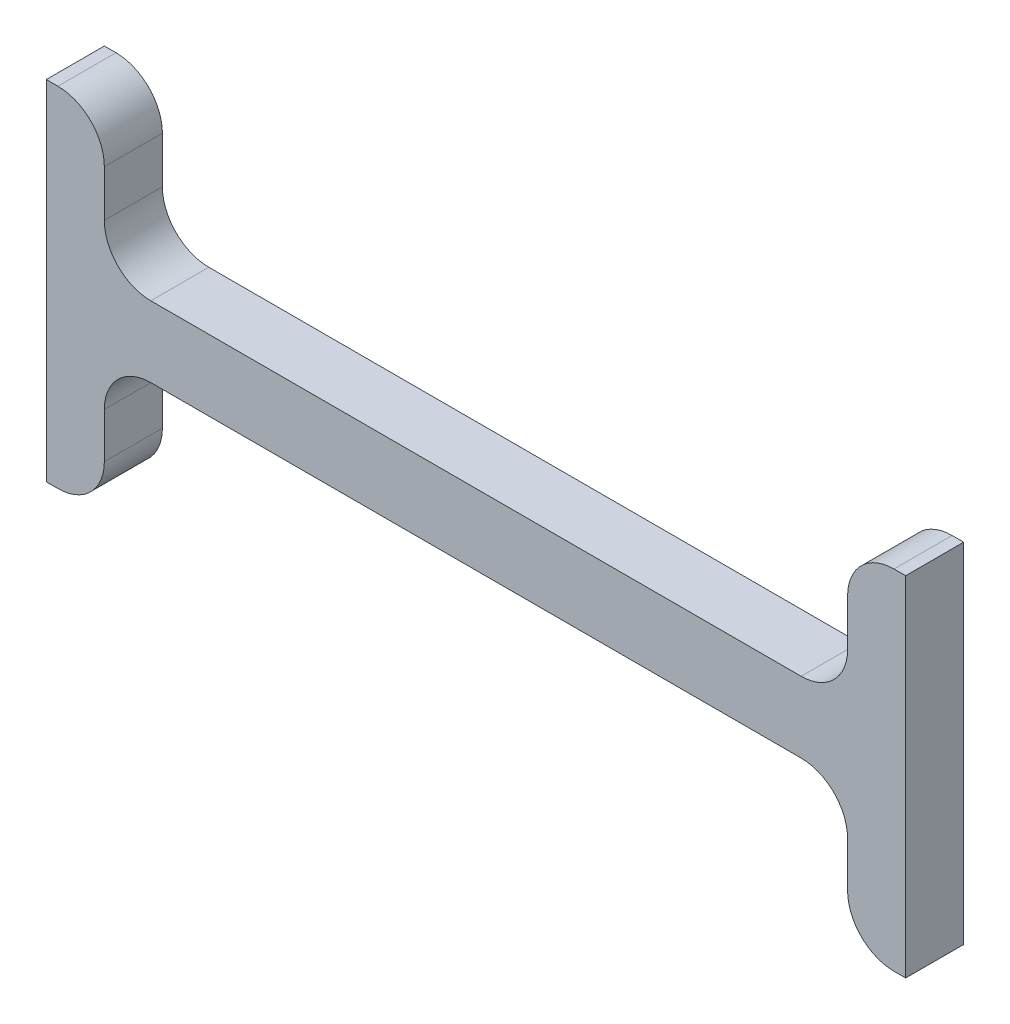
SolidWorks part; units mm, degrees
ref_plane "Front Plane" through (0, 0, 0) normal (0, 0, 1) x (1, 0, 0)
ref_plane "Top Plane" through (0, 0, 0) normal (0, 1, 0) x (1, 0, 0)
ref_plane "Right Plane" through (0, 0, 0) normal (1, 0, 0) x (0, 0, -1)
sketch "Sketch3" plane through (0, 0, 0) normal (0, 0, 1) x (1, 0, 0)
  line L0 (0, 0) -> (0, 38.1)
  line L1 (93.98, 0) -> (93.98, 38.1)
  line L2 (0, 19.05) -> (93.98, 19.05) construction
  line L3 (6.35, 5.08) -> (6.35, 10.033)
  line L4 (11.43, 15.113) -> (82.55, 15.113)
  line L5 (11.43, 22.86) -> (82.55, 22.86)
  line L6 (87.63, 5.08) -> (87.63, 10.033)
  line L7 (0, 38.1) -> (1.27, 38.1)
  line L8 (1.27, 0) -> (0, 0)
  line L9 (92.71, 0) -> (93.98, 0)
  line L10 (93.98, 38.1) -> (92.71, 38.1)
  line L11 (6.35, 27.94) -> (6.35, 33.02)
  line L12 (0, 22.86) -> (93.98, 22.86) construction
  line L13 (87.63, 27.94) -> (87.63, 33.02)
  line L14 (6.35, 0) -> (6.35, 38.1) construction
  line L15 (0, 15.113) -> (93.98, 15.113) construction
  line L17 (87.63, 0) -> (87.63, 38.1) construction
  arc A0 (6.35, 5.08) -> (1.27, 0) centre (1.27, 5.08) cw
  arc A1 (87.63, 5.08) -> (92.71, 0) centre (92.71, 5.08) ccw
  arc A2 (87.63, 33.02) -> (92.71, 38.1) centre (92.71, 33.02) cw
  arc A3 (87.63, 10.033) -> (82.55, 15.113) centre (82.55, 10.033) ccw
  arc A4 (87.63, 27.94) -> (82.55, 22.86) centre (82.55, 27.94) cw
  arc A5 (6.35, 10.033) -> (11.43, 15.113) centre (11.43, 10.033) cw
  arc A6 (11.43, 22.86) -> (6.35, 27.94) centre (11.43, 27.94) cw
  arc A7 (6.35, 33.02) -> (1.27, 38.1) centre (1.27, 33.02) ccw
  point P36 (6.35, 22.86)
  dimension "D7" = 5.08
  dimension "D1" = 38.1
  dimension "D2" = 93.98
  dimension "D3" = 6.35
  dimension "D4" = 6.35
  dimension "D5" = 3.937
  dimension "D6" = 3.81
extrude "Boss-Extrude2" add sketch "Sketch3" along normal blind 6.35
